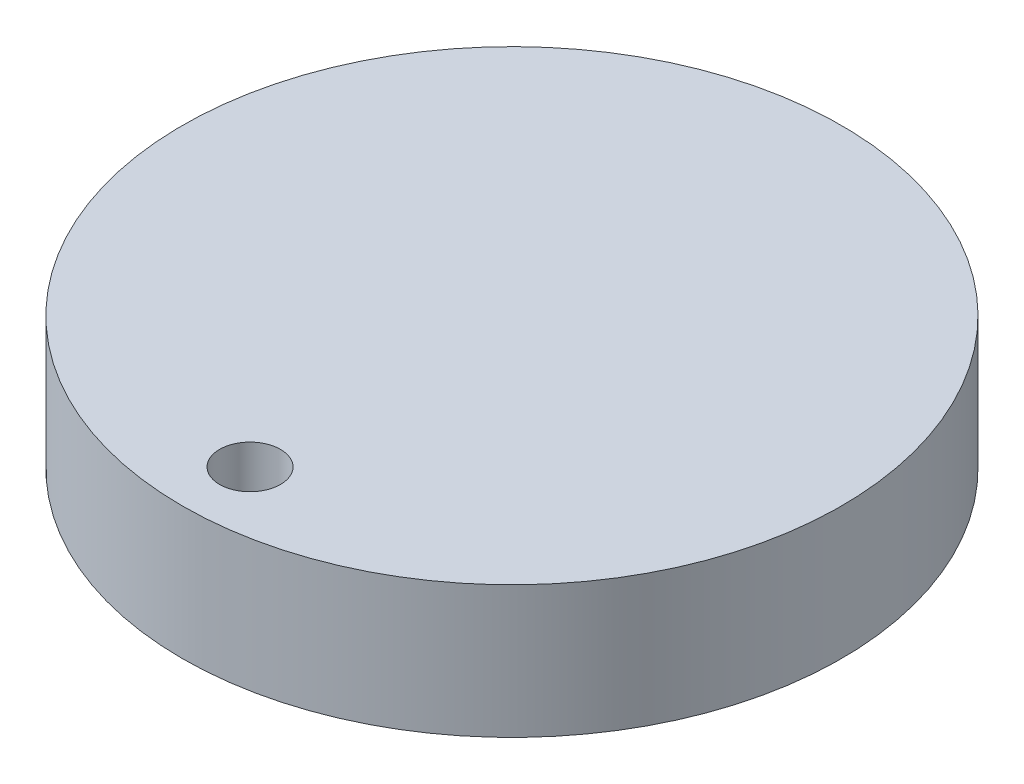
SolidWorks part; units mm, degrees
ref_plane "Front Plane" through (0, 0, 0) normal (0, 0, 1) x (1, 0, 0)
ref_plane "Top Plane" through (0, 0, 0) normal (0, 1, 0) x (1, 0, 0)
ref_plane "Right Plane" through (0, 0, 0) normal (1, 0, 0) x (0, 0, -1)
sketch "Sketch1" plane through (0, 0, 0) normal (0, 1, 0) x (1, 0, 0)
  circle A2 centre (0, 0) radius 12.6629
  circle A3 centre (0, -10.0625) radius 1.1697
extrude "Boss-Extrude3" add sketch "Sketch1" along normal blind 5.08
